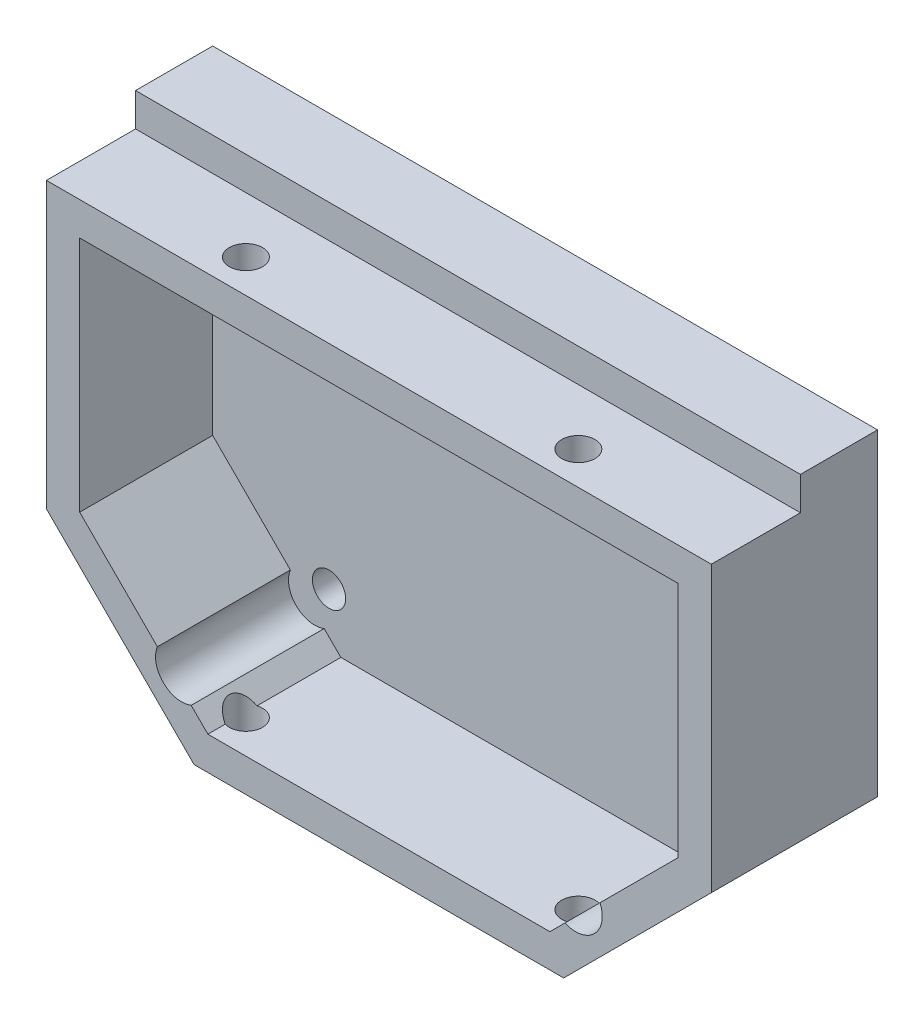
SolidWorks part; units mm, degrees
ref_plane "Plan de face" through (0, 0, 0) normal (0, 0, 1) x (1, 0, 0)
ref_plane "Plan de dessus" through (0, 0, 0) normal (0, 1, 0) x (1, 0, 0)
ref_plane "Plan de droite" through (0, 0, 0) normal (1, 0, 0) x (0, 0, -1)
sketch "Esquisse1" plane through (0, 0, 0) normal (0, 0, 1) x (1, 0, 0)
  line L0 (44.1184, 33.6676) -> (51.9493, 33.6676)
  line L1 (-48.0507, 33.6676) -> (44.1184, 33.6676)
  line L2 (-48.0507, 33.6676) -> (-48.0507, -9.1246)
  line L3 (-25.8429, -31.3324) -> (29.7415, -31.3324)
  line L4 (-48.0507, -9.1246) -> (-25.8429, -31.3324)
  line L5 (51.9493, 33.6676) -> (51.9493, -9.1246)
  line L6 (29.7415, -31.3324) -> (51.9493, -9.1246)
  point P6 (51.9493, 33.6676)
  dimension "D1" = 100
extrude "Boss.-Extru.1" add sketch "Esquisse1" along normal blind 13 and the other way blind 12
shell "Coque1" thickness 5
sketch "Esquisse3" plane through (0, -31.3324, 0) normal (0, -1, 0) x (1, 0, 0)
  line L1 (51.9493, 13) -> (51.9493, -12) construction
  line L4 (-25.8429, 13) -> (29.7415, 13) construction
  line L5 (-48.0507, 13) -> (-48.0507, -12) construction
  circle A0 centre (-23.0507, 8) radius 2.5
  circle A1 centre (26.9493, 8) radius 2.5
  point P11 (51.9493, 0.5)
  dimension "D1" = 5
  dimension "D2" = 5
  dimension "D5" = 25
  dimension "D3" = 5
  dimension "D4" = 5
  dimension "D6" = 25
extrude "Enlèv. mat.-Extru.2" cut sketch "Esquisse3" against normal up to surface (65 mm away) up to face at (1.9493, 33.6676, 0.5)
sketch "Esquisse5" plane through (0, 0, -7) normal (0, 0, 1) x (1, 0, 0)
  line L0 (51.9493, 33.6676) -> (-48.0507, 33.6676) construction
  line L1 (-48.0507, 33.6676) -> (-48.0507, -9.1246) construction
  circle A0 centre (-25.5507, 23.6676) radius 2.5
  dimension "D1" = 5
  dimension "D2" = 22.5
  dimension "D4" = 10
extrude "Enlèv. mat.-Extru.3" cut sketch "Esquisse5" against normal up to surface (5 mm away) up to face at (1.9493, -2.2631, -12)
pattern_linear "Répétition linéaire1" count 2 spacing 55 along (1, 0, 0) count 2 spacing 42 along (0, -1, 0) of "Enlèv. mat.-Extru.3"
sketch "Esquisse6" plane through (0, 0, 13) normal (0, 0, 1) x (1, 0, 0)
  line L0 (35.2047, -18.7981) -> (29.9373, -24.0655)
  line L1 (-43.0507, -7.0535) -> (-23.7718, -26.3324) construction
  line L2 (-43.0507, -7.0535) -> (-23.7718, -26.3324) construction
  line L3 (27.6704, -26.3324) -> (46.9493, -7.0535) construction
  line L4 (-31.3659, -18.7383) -> (-26.2792, -23.825)
  line L5 (27.6704, -26.3324) -> (46.9493, -7.0535) construction
  arc A0 (-26.2792, -23.825) -> (-31.3659, -18.7383) centre (-27.7219, -20.181) cw
  arc A1 (35.2047, -18.7981) -> (29.9373, -24.0655) centre (31.5473, -20.4081) cw
extrude "Enlèv. mat.-Extru.4" cut sketch "Esquisse6" against normal up to surface (20 mm away) up to face at (31.9493, -18.3324, -7)
sketch "Esquisse8" plane through (0, 33.6676, 0) normal (0, 1, 0) x (1, 0, 0)
  line L0 (51.9493, 12) -> (51.9493, -13) construction
  line L1 (-48.0507, 12) -> (51.9493, 12)
  line L2 (-48.0507, 12) -> (-48.0507, 0.4)
  line L3 (-48.0507, 0.4) -> (51.9493, 0.4)
  line L4 (51.9493, 12) -> (51.9493, 0.4)
  dimension "D1" = 11.6
extrude "Boss.-Extru.2" add sketch "Esquisse8" along normal blind 5
